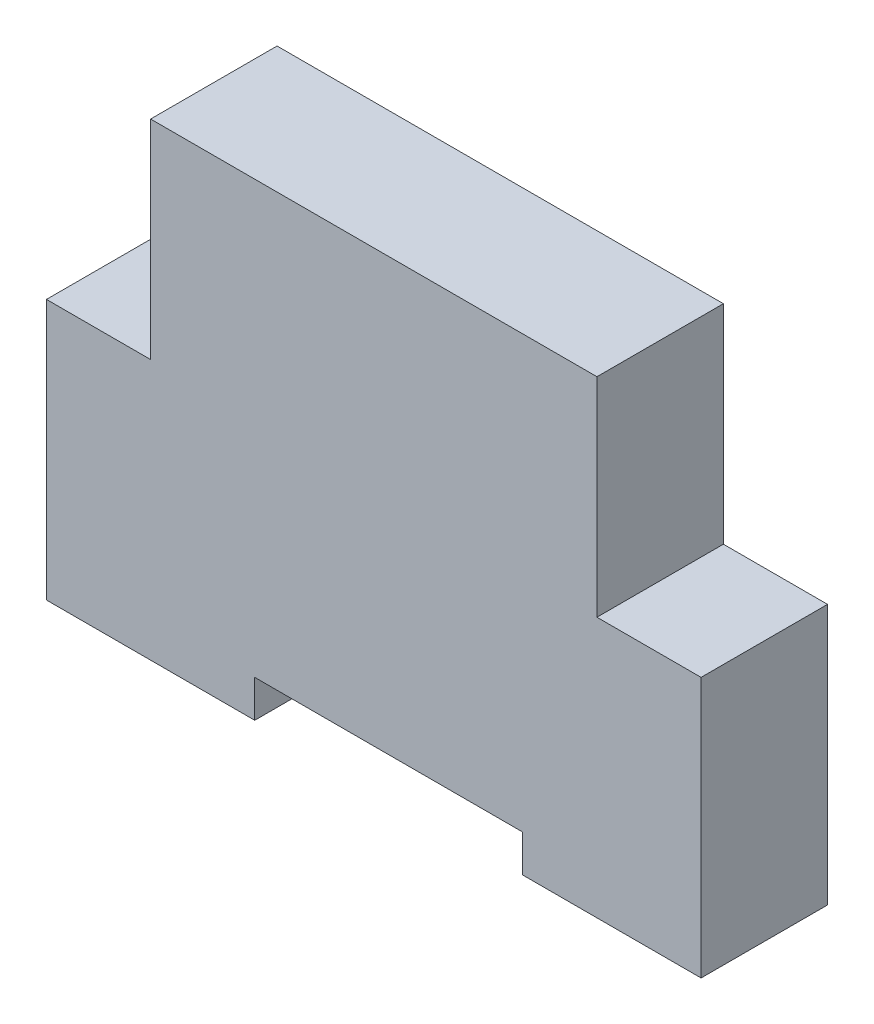
SolidWorks part; units mm, degrees
ref_plane "Front Plane" through (0, 0, 0) normal (0, 0, 1) x (1, 0, 0)
ref_plane "Top Plane" through (0, 0, 0) normal (0, 1, 0) x (1, 0, 0)
ref_plane "Right Plane" through (0, 0, 0) normal (1, 0, 0) x (0, 0, -1)
sketch "Sketch1" plane through (0, 0, 0) normal (0, 0, 1) x (1, 0, 0)
  line L0 (-32, 58) -> (28, 58)
  line L1 (28, 58) -> (28, 30)
  line L2 (28, 30) -> (42, 30)
  line L3 (42, 30) -> (42, -5)
  line L4 (42, -5) -> (18, -5)
  line L5 (18, -5) -> (18, 0)
  line L6 (18, 0) -> (-18, 0)
  line L7 (-18, 0) -> (-18, -5)
  line L8 (-18, -5) -> (-46, -5)
  line L9 (-46, -5) -> (-46, 30)
  line L10 (-46, 30) -> (-32, 30)
  line L11 (-32, 30) -> (-32, 58)
  point P11 (0, 0)
  dimension "D1" = 28
  dimension "D2" = 24
  dimension "D3" = 36
  dimension "D4" = 58
  dimension "D5" = 5
  dimension "D6" = 60
  dimension "D7" = 35
extrude "Boss-Extrude1" add sketch "Sketch1" along normal blind 17
